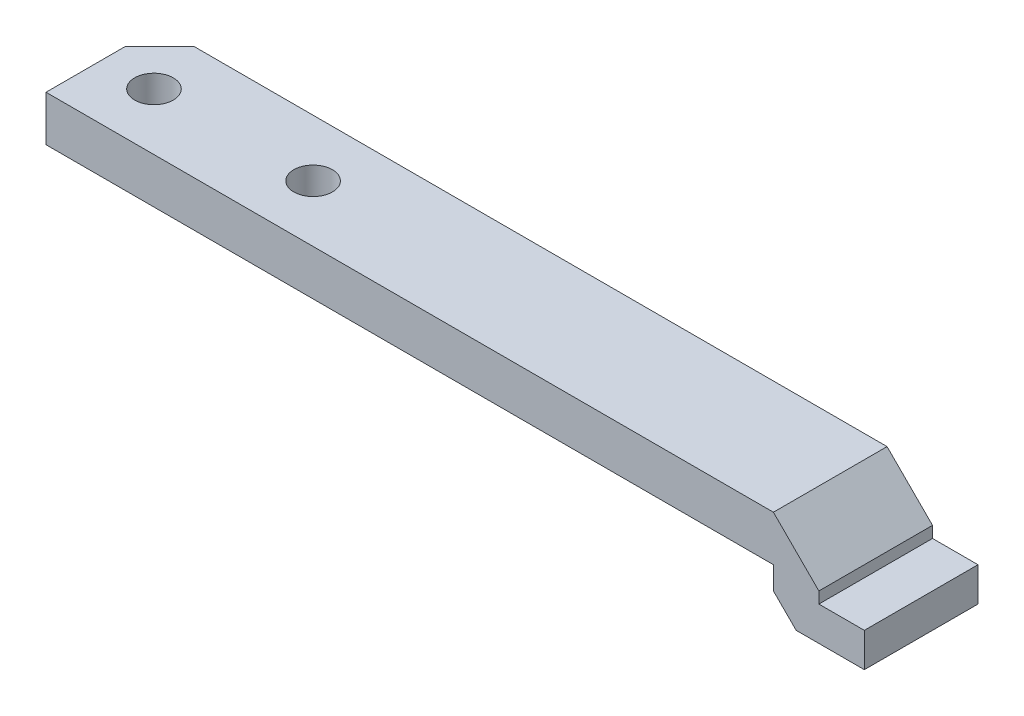
SolidWorks part; units mm, degrees
ref_plane "Front Plane" through (0, 0, 0) normal (0, 0, 1) x (1, 0, 0)
ref_plane "Top Plane" through (0, 0, 0) normal (0, 1, 0) x (1, 0, 0)
ref_plane "Right Plane" through (0, 0, 0) normal (1, 0, 0) x (0, 0, -1)
sketch "Sketch2" plane through (0, 0, 0) normal (0, 0, 1) x (1, 0, 0)
  line L0 (-41.6686, 7.4977) -> (-41.6686, 3.4977)
  line L1 (-41.6686, 3.4977) -> (22.3314, 3.4977)
  line L2 (22.3314, 3.4977) -> (22.3314, -0.5023)
  line L3 (22.3314, -0.5023) -> (30.3314, -0.5023)
  line L4 (30.3314, -0.5023) -> (30.3314, 2.4977)
  line L5 (30.3314, 2.4977) -> (26.3314, 2.4977)
  line L6 (26.3314, 2.4977) -> (26.3314, 7.4977)
  line L7 (26.3314, 7.4977) -> (-41.6686, 7.4977)
  point P6 (0, 0)
  point P9 (-21.5587, 5.3523)
  dimension "D1" = 4
  dimension "D2" = 64
  dimension "D3" = 68
  dimension "D4" = 3
  dimension "D5" = 8
  dimension "D6" = 4
  dimension "D7" = 5
extrude "Boss-Extrude1" add sketch "Sketch2" along normal blind 10 contours L7 L0 L1 L2 L3 L4 L5 L6
chamfer "Chamfer1" distance 3 angle 45 1 edges at (-41.6686, 5.4977, 0)
chamfer "Chamfer4" distance 4 angle 45 1 edges at (26.3314, 7.4977, 5)
chamfer "Chamfer5" distance 2 angle 45 1 edges at (22.3314, -0.5023, 5)
sketch "Sketch4" plane through (0, 7.4977, 0) normal (0, 1, 0) x (1, 0, 0)
  line L0 (-41.6686, -10) -> (-41.6686, -3) construction
  line L1 (22.3314, 0) -> (-38.6686, 0) construction
  circle A0 centre (-37.1686, -5) radius 1.7
  circle A1 centre (-23.1686, -5) radius 1.7
  point P6 (0, 0)
  point P9 (0, 0)
  dimension "D5" = 3.4
  dimension "D1" = 4.5
  dimension "D2" = 14
  dimension "D3" = 5
  dimension "D4" = 5
extrude "Cut-Extrude1" cut sketch "Sketch4" against normal up to next contours A0 | A1
